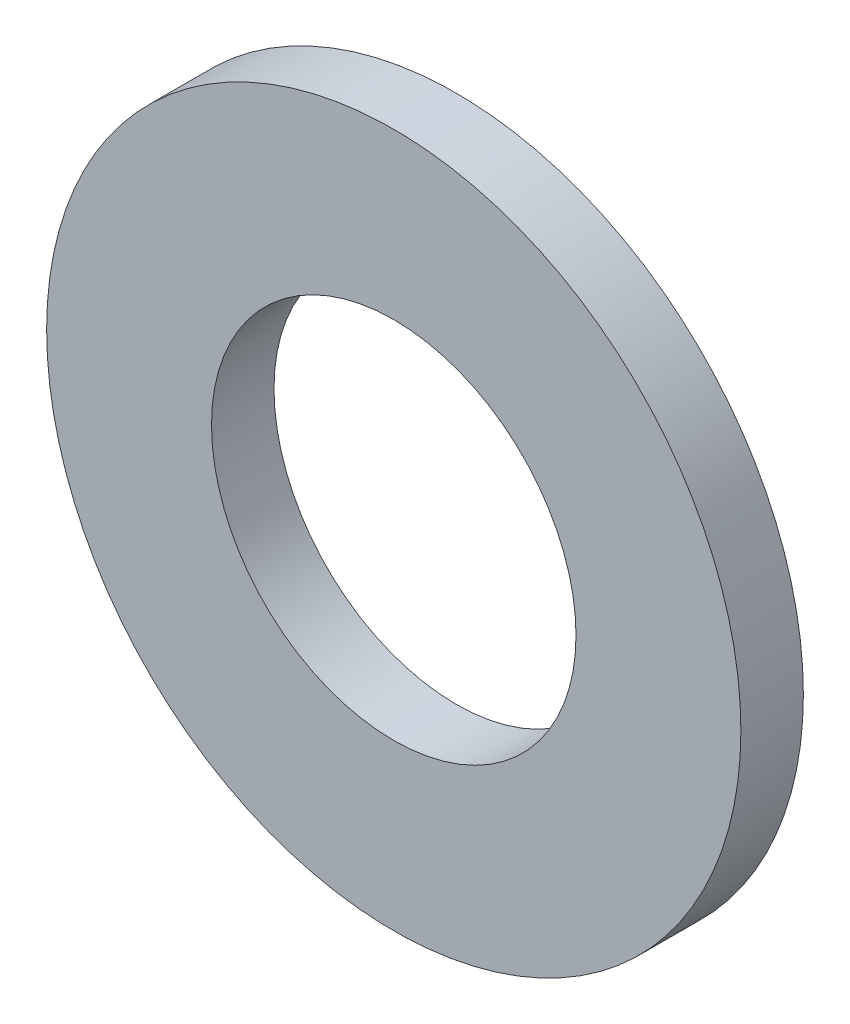
SolidWorks part; units mm, degrees
ref_plane "Front Plane" through (0, 0, 0) normal (0, 0, 1) x (1, 0, 0)
ref_plane "Top Plane" through (0, 0, 0) normal (0, 1, 0) x (1, 0, 0)
ref_plane "Right Plane" through (0, 0, 0) normal (1, 0, 0) x (0, 0, -1)
sketch "Sketch1" plane through (0, 0, 0) normal (0, 0, 1) x (1, 0, 0)
  circle A0 centre (0, 0) radius 5.25
  circle A1 centre (0, 0) radius 10
  dimension "ID" = 10.5
  dimension "OD" = 20
extrude "Extrude1" add sketch "Sketch1" against normal blind 1.8
